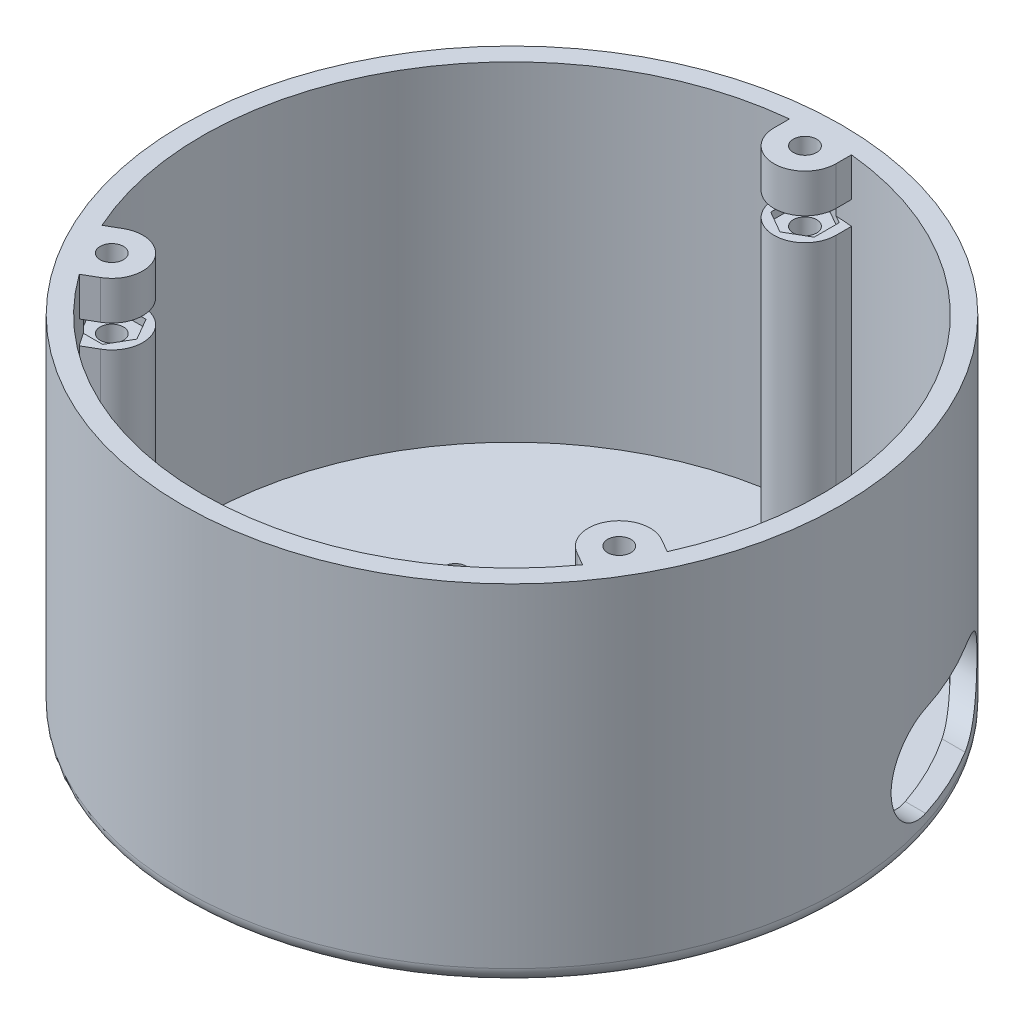
SolidWorks part; units mm, degrees
ref_plane "Front Plane" through (0, 0, 0) normal (0, 0, 1) x (1, 0, 0)
ref_plane "Top Plane" through (0, 0, 0) normal (0, 1, 0) x (1, 0, 0)
ref_plane "Right Plane" through (0, 0, 0) normal (1, 0, 0) x (0, 0, -1)
sketch "Sketch1" plane through (0, 0, 0) normal (0, 1, 0) x (1, 0, 0)
  circle A0 centre (0, 0) radius 42.5
  dimension "D1" = 85
extrude "Boss-Extrude1" add sketch "Sketch1" along normal blind 45
fillet "Fillet1" radius 2 1 edges at (0, 0, 42.5)
shell "Shell1" thickness 2.5
sketch "Sketch2" plane through (0, 2.5, 0) normal (0, 1, 0) x (1, 0, 0)
  line L0 (0, 0) -> (0, 37.8) construction
  line L1 (0, 0) -> (-32.7358, -18.9) construction
  line L2 (0, 0) -> (32.7358, -18.9) construction
  line L3 (-34.0809, -24.2954) -> (-30.7358, -22.3641)
  line L4 (-34.0809, -24.2954) -> (-38.0809, -17.3672)
  line L5 (-38.0809, -17.3672) -> (-34.7358, -15.4359)
  line L6 (-34.7358, -15.4359) -> (-30.7358, -22.3641) construction
  line L7 (38.0809, -17.3672) -> (34.7358, -15.4359)
  line L8 (38.0809, -17.3672) -> (34.0809, -24.2954)
  line L9 (34.0809, -24.2954) -> (30.7358, -22.3641)
  line L10 (30.7358, -22.3641) -> (34.7358, -15.4359) construction
  line L11 (-4, 41.6627) -> (-4, 37.8)
  line L12 (-4, 41.6627) -> (4, 41.6627)
  line L13 (4, 41.6627) -> (4, 37.8)
  line L14 (4, 37.8) -> (-4, 37.8) construction
  arc A3 (-34.7358, -15.4359) -> (-30.7358, -22.3641) centre (-32.7358, -18.9) cw
  arc A4 (30.7358, -22.3641) -> (34.7358, -15.4359) centre (32.7358, -18.9) cw
  arc A5 (4, 37.8) -> (-4, 37.8) centre (0, 37.8) cw
  circle A6 centre (-32.7358, -18.9) radius 1.5
  circle A7 centre (0, 37.8) radius 1.5
  circle A8 centre (32.7358, -18.9) radius 1.5
  point P3 (-32.7358, -18.9)
  point P11 (32.7358, -18.9)
  point P17 (0, 37.8)
  dimension "D3" = 4
  dimension "D5" = 3
  dimension "D1" = 120
  dimension "D2" = 120
  dimension "D4" = 37.8
extrude "Boss-Extrude2" add sketch "Sketch2" along normal up to surface (42.5 mm away) up to face at (0, 45, 40)
sketch "Sketch3" plane through (0, 45, 0) normal (0, 1, 0) x (1, 0, 0)
  line L1 (-31.1192, -16.1) -> (-34.3523, -16.1)
  line L2 (-34.3523, -16.1) -> (-35.9689, -18.9)
  line L3 (-35.9689, -18.9) -> (-34.3523, -21.7)
  line L4 (-34.3523, -21.7) -> (-31.1192, -21.7)
  line L5 (-31.1192, -21.7) -> (-29.5026, -18.9)
  line L6 (-29.5026, -18.9) -> (-31.1192, -16.1)
  line L7 (0, 41.0332) -> (-2.8, 39.4166)
  line L8 (-2.8, 39.4166) -> (-2.8, 36.1834)
  line L9 (-2.8, 36.1834) -> (0, 34.5668)
  line L10 (0, 34.5668) -> (2.8, 36.1834)
  line L11 (2.8, 36.1834) -> (2.8, 39.4166)
  line L12 (2.8, 39.4166) -> (0, 41.0332)
  line L13 (34.3523, -16.1) -> (31.1192, -16.1)
  line L14 (31.1192, -16.1) -> (29.5026, -18.9)
  line L15 (29.5026, -18.9) -> (31.1192, -21.7)
  line L16 (31.1192, -21.7) -> (34.3523, -21.7)
  line L17 (34.3523, -21.7) -> (35.9689, -18.9)
  line L18 (35.9689, -18.9) -> (34.3523, -16.1)
  circle A0 centre (-32.7358, -18.9) radius 2.8 construction
  circle A1 centre (0, 37.8) radius 2.8 construction
  circle A2 centre (32.7358, -18.9) radius 2.8 construction
  arc A3 (-4, 37.8) -> (4, 37.8) centre (0, 37.8) ccw construction
  arc A4 (-30.7358, -22.3641) -> (-34.7358, -15.4359) centre (-32.7358, -18.9) ccw construction
  dimension "D1" = 5.6
extrude "Cut-Extrude1" cut sketch "Sketch3" against normal blind 6 from offset 3 offset against normal yes
sketch "Sketch4" plane through (0, 45, 0) normal (0, 1, 0) x (1, 0, 0)
  circle A0 centre (0, 0) radius 40
extrude "Cut-Extrude2" cut sketch "Sketch4" against normal blind 3 from offset 5 offset against normal yes
sketch "Sketch6" plane through (0, 0, 0) normal (1, 0, 0) x (0, 0, -1)
  line L0 (12.8585, 9) -> (22.2415, 9) construction
  line L1 (12.8585, 14.8643) -> (22.2415, 14.8643)
  line L2 (12.8585, 3.1357) -> (22.2415, 3.1357)
  arc A0 (12.8585, 14.8643) -> (12.8585, 3.1357) centre (12.8585, 9) ccw
  arc A1 (22.2415, 3.1357) -> (22.2415, 14.8643) centre (22.2415, 9) ccw
  point P2 (17.55, 9)
  dimension "D1" = 17.55
  dimension "D2" = 9
extrude "Cut-Extrude3" cut sketch "Sketch6" along normal blind 120
sketch "Sketch7" plane through (0, 0, 0) normal (0, -1, 0) x (1, 0, 0)
  line L0 (0, 20) -> (0, 0) construction
  line L1 (0, 0) -> (-17.3205, -10) construction
  line L2 (0, 0) -> (17.3205, -10) construction
  circle A0 centre (17.3205, -10) radius 1.5
  circle A1 centre (0, 20) radius 1.5
  circle A2 centre (-17.3205, -10) radius 1.5
  dimension "D1" = 3
  dimension "D2" = 20
  dimension "D3" = 120
  dimension "D4" = 120
extrude "Cut-Extrude4" cut sketch "Sketch7" against normal blind 10
